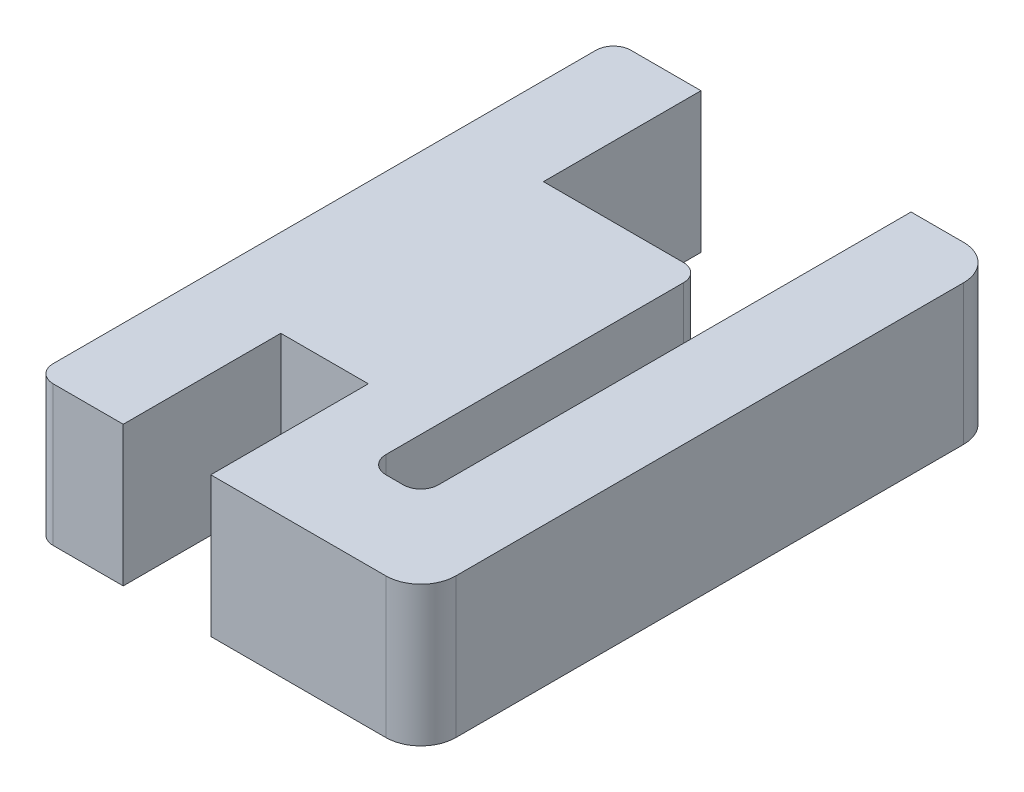
SolidWorks part; units mm, degrees
ref_plane "Alzado" through (0, 0, 0) normal (0, 0, 1) x (1, 0, 0)
ref_plane "Planta" through (0, 0, 0) normal (0, 1, 0) x (1, 0, 0)
ref_plane "Vista lateral" through (0, 0, 0) normal (1, 0, 0) x (0, 0, -1)
sketch "Croquis1" plane through (0, 0, 0) normal (0, 1, 0) x (1, 0, 0)
  line L0 (2.5, 12) -> (2.5, 16.5)
  line L1 (0, 0) -> (2.5, 0)
  line L2 (0, 0) -> (0, 16.5)
  line L3 (0, 16.5) -> (2.5, 16.5)
  line L4 (2.5, 0) -> (2.5, 4.5)
  line L5 (2.5, 12) -> (7, 12)
  line L7 (2.5, 4.5) -> (5, 4.5)
  line L9 (5, 4.5) -> (5, 0)
  line L10 (5, 0) -> (11, 0)
  line L11 (11, 0) -> (11, 16.5)
  line L12 (11, 16.5) -> (8.5, 16.5)
  line L13 (8.5, 16.5) -> (8.5, 2.5)
  line L14 (8.5, 2.5) -> (7, 2.5)
  line L15 (7, 2.5) -> (7, 12)
  line L18 (5, 4.5) -> (5, 0)
  point P9 (1.25, 16.5)
  point P10 (4.7817, 12)
  dimension "D1" = 16.5
  dimension "D2" = 2.5
  dimension "D3" = 2.5
  dimension "D4" = 4.5
  dimension "D5" = 2.5
  dimension "D6" = 7.5
  dimension "D7" = 1.5
  dimension "D8" = 16.5
  dimension "D9" = 2.5
  dimension "D10" = 2
extrude "Saliente-Extruir1" add sketch "Croquis1" along normal blind 4 contours L14 L15 L5 L0 L3 L2 L1 L4 L7 L9 L10 L11 L12 L13
fillet "Redondeo1" radius 0.5 5 edges at (8.5, 2, -2.5) (7, 2, -2.5) (7, 2, -12) (0, 2, 0) (0, 2, -16.5)
fillet "Redondeo2" radius 1 2 edges at (11, 2, 0) (11, 2, -16.5)
